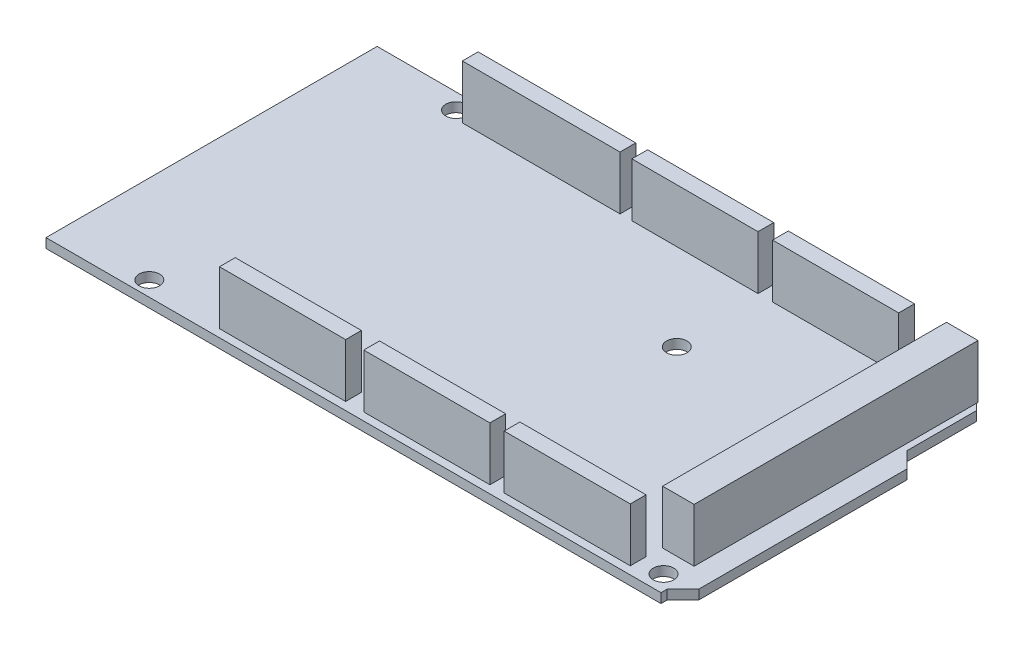
SolidWorks part; units mm, degrees
ref_plane "Front Plane" through (0, 0, 0) normal (0, 0, 1) x (1, 0, 0)
ref_plane "Top Plane" through (0, 0, 0) normal (0, 1, 0) x (1, 0, 0)
ref_plane "Right Plane" through (0, 0, 0) normal (1, 0, 0) x (0, 0, -1)
sketch "Sketch1" plane through (0, 0, 0) normal (0, 1, 0) x (1, 0, 0)
  line L0 (99.06, 39.608) -> (101.6, 37.068)
  line L1 (0, 0) -> (99.06, 0)
  line L2 (0, 0) -> (0, 53.34)
  line L3 (0, 53.34) -> (96.52, 53.34)
  line L4 (99.06, 0) -> (99.06, 1)
  line L5 (101.6, 37.068) -> (101.6, 3.54)
  line L6 (101.6, 3.54) -> (99.06, 1)
  line L7 (99.06, 39.608) -> (99.06, 50.8)
  line L8 (96.52, 53.34) -> (99.06, 50.8)
  point P1 (99.06, 53.34)
  dimension "D1" = 99.06
  dimension "D2" = 53.34
  dimension "D3" = 101.6
  dimension "D4" = 38.608
  dimension "D5" = 1
extrude "Boss-Extrude1" add sketch "Sketch1" along normal mid plane 1.524
hole_wizard "Ø1.3 (1.3) Diameter Hole1" positions "Sketch2" profile "Sketch3" hole size "Ø1.3" standard "ANSI Metric" end condition up to next
sketch "Sketch2" plane through (0, 0.762, 0) normal (0, 1, 0) x (1, 0, 0)
  line L0 (0, 53.34) -> (0, 0) construction
  line L1 (0, 0) -> (99.06, 0) construction
  line L2 (27.94, 0) -> (27.94, 2.54) construction
  line L5 (18.796, 50.8) -> (18.796, 53.34) construction
  line L6 (96.52, 53.34) -> (0, 53.34) construction
  line L9 (18.796, 50.8) -> (21.336, 50.8) construction
  line L10 (51.181, 2.54) -> (53.721, 2.54) construction
  line L11 (46.101, 50.8) -> (48.641, 50.8) construction
  line L12 (73.787, 2.54) -> (76.327, 2.54) construction
  point P0 (27.94, 2.54)
  point P2 (18.796, 50.8)
  point P25 (30.48, 2.54)
  point P26 (33.02, 2.54)
  point P27 (35.56, 2.54)
  point P28 (38.1, 2.54)
  point P29 (40.64, 2.54)
  point P30 (43.18, 2.54)
  point P31 (45.72, 2.54)
  point P36 (21.336, 50.8)
  point P37 (23.876, 50.8)
  point P38 (26.416, 50.8)
  point P39 (28.956, 50.8)
  point P40 (31.496, 50.8)
  point P41 (34.036, 50.8)
  point P42 (36.576, 50.8)
  point P43 (39.116, 50.8)
  point P44 (41.656, 50.8)
  point P47 (51.181, 2.54)
  point P49 (46.101, 50.8)
  point P56 (53.721, 2.54)
  point P57 (56.261, 2.54)
  point P58 (58.801, 2.54)
  point P59 (61.341, 2.54)
  point P60 (63.881, 2.54)
  point P61 (66.421, 2.54)
  point P62 (68.961, 2.54)
  point P71 (48.641, 50.8)
  point P72 (51.181, 50.8)
  point P73 (53.721, 50.8)
  point P74 (56.261, 50.8)
  point P75 (58.801, 50.8)
  point P76 (61.341, 50.8)
  point P77 (63.881, 50.8)
  point P80 (68.7578, 50.8)
  point P82 (73.787, 2.54)
  point P93 (71.2978, 50.8)
  point P94 (76.327, 2.54)
  point P95 (73.8378, 50.8)
  point P96 (78.867, 2.54)
  point P97 (76.3778, 50.8)
  point P98 (81.407, 2.54)
  point P99 (78.9178, 50.8)
  point P100 (83.947, 2.54)
  point P101 (81.4578, 50.8)
  point P102 (86.487, 2.54)
  point P103 (83.9978, 50.8)
  point P104 (89.027, 2.54)
  point P105 (86.5378, 50.8)
  point P106 (91.567, 2.54)
  point P109 (94.234, 50.8)
  point P111 (96.774, 50.8)
  point P122 (94.234, 48.26)
  point P123 (96.774, 48.26)
  point P124 (94.234, 45.72)
  point P125 (96.774, 45.72)
  point P126 (94.234, 43.18)
  point P127 (96.774, 43.18)
  point P128 (94.234, 40.64)
  point P129 (96.774, 40.64)
  point P130 (94.234, 38.1)
  point P131 (96.774, 38.1)
  point P132 (94.234, 35.56)
  point P133 (96.774, 35.56)
  point P134 (94.234, 33.02)
  point P135 (96.774, 33.02)
  point P136 (94.234, 30.48)
  point P137 (96.774, 30.48)
  point P138 (94.234, 27.94)
  point P139 (96.774, 27.94)
  point P140 (94.234, 25.4)
  point P141 (96.774, 25.4)
  point P142 (94.234, 22.86)
  point P143 (96.774, 22.86)
  point P144 (94.234, 20.32)
  point P145 (96.774, 20.32)
  point P146 (94.234, 17.78)
  point P147 (96.774, 17.78)
  point P148 (94.234, 15.24)
  point P149 (96.774, 15.24)
  point P150 (94.234, 12.7)
  point P151 (96.774, 12.7)
  point P152 (94.234, 10.16)
  point P153 (96.774, 10.16)
  point P154 (94.234, 7.62)
  point P155 (96.774, 7.62)
  dimension "D1" = 18.796
  dimension "D2" = 50.8
  dimension "D3" = 27.94
  dimension "D5" = 2.54
  dimension "D7" = 2.54
  dimension "D8" = 51.181
  dimension "D10" = 2.54
  dimension "D11" = 46.101
  dimension "D12" = 8
  dimension "D13" = 2.54
  dimension "D14" = 73.787
  dimension "D15" = 68.7578
  dimension "D17" = 2.54
  dimension "D18" = 2.54
  dimension "D20" = 94.234
  dimension "D4" = 8
  dimension "D6" = 10
  dimension "D9" = 8
  dimension "D16" = 8
  dimension "D19" = 18
sketch "Sketch3" plane through (27.94, 0.762, -2.54) normal (1, 0, 0) x (0, 0, 1)
  line L0 (0, 0) -> (0, 1.524)
  line L1 (0, 1.524) -> (0.65, 1.524)
  line L2 (0.65, 1.524) -> (0.65, 0)
  line L5 (0.65, 0) -> (0, 0)
  line L11 (0, -6.35) -> (0, 107.95) construction
  dimension "Thru Hole Dia." = 1.3
  dimension "Thru Hole Depth" = 1.524
hole_wizard "Ø3.3 (3.3) Diameter Hole1" positions "Sketch4" profile "Sketch5" hole size "Ø3.3" standard "ANSI Metric" end condition up to next
sketch "Sketch4" plane through (0, 0.762, 0) normal (0, 1, 0) x (1, 0, 0)
  line L0 (0, 53.34) -> (0, 0) construction
  line L1 (0, 0) -> (99.06, 0) construction
  point P0 (15.24, 50.8)
  point P2 (90.3732, 50.8)
  point P4 (96.647, 2.8094)
  point P6 (66.04, 7.366)
  point P8 (66.04, 35.56)
  point P10 (14.224, 2.413)
  dimension "D1" = 14.224
  dimension "D2" = 2.413
  dimension "D3" = 7.366
  dimension "D4" = 66.04
  dimension "D5" = 35.56
  dimension "D6" = 96.647
  dimension "D7" = 15.24
  dimension "D8" = 90.3732
  dimension "D9" = 50.8
sketch "Sketch5" plane through (15.24, 0.762, -50.8) normal (1, 0, 0) x (0, 0, 1)
  line L0 (0, 0) -> (0, 1.524)
  line L1 (0, 1.524) -> (1.65, 1.524)
  line L2 (1.65, 1.524) -> (1.65, 0)
  line L5 (1.65, 0) -> (0, 0)
  line L11 (0, -6.35) -> (0, 107.95) construction
  dimension "Thru Hole Dia." = 3.3
  dimension "Thru Hole Depth" = 1.524
sketch "Sketch6" plane through (0, 0.762, 0) normal (0, 1, 0) x (1, 0, 0)
  line L1 (17.526, 52.07) -> (42.926, 52.07)
  line L2 (17.526, 52.07) -> (17.526, 49.53)
  line L3 (17.526, 49.53) -> (42.926, 49.53)
  line L4 (42.926, 52.07) -> (42.926, 49.53)
  line L5 (44.831, 52.07) -> (65.151, 52.07)
  line L6 (44.831, 52.07) -> (44.831, 49.53)
  line L7 (44.831, 49.53) -> (65.151, 49.53)
  line L8 (65.151, 52.07) -> (65.151, 49.53)
  line L9 (67.4878, 52.07) -> (87.8078, 52.07)
  line L10 (67.4878, 52.07) -> (67.4878, 49.53)
  line L11 (67.4878, 49.53) -> (87.8078, 49.53)
  line L12 (87.8078, 52.07) -> (87.8078, 49.53)
  line L13 (92.964, 52.07) -> (98.044, 52.07)
  line L14 (92.964, 52.07) -> (92.964, 6.35)
  line L15 (92.964, 6.35) -> (98.044, 6.35)
  line L16 (98.044, 52.07) -> (98.044, 6.35)
  line L17 (92.837, 1.27) -> (72.517, 1.27)
  line L18 (92.837, 1.27) -> (92.837, 3.81)
  line L19 (92.837, 3.81) -> (72.517, 3.81)
  line L20 (72.517, 1.27) -> (72.517, 3.81)
  line L21 (26.67, 3.81) -> (46.99, 3.81)
  line L22 (26.67, 3.81) -> (26.67, 1.27)
  line L23 (26.67, 1.27) -> (46.99, 1.27)
  line L24 (46.99, 3.81) -> (46.99, 1.27)
  line L25 (49.911, 3.81) -> (70.231, 3.81)
  line L26 (49.911, 3.81) -> (49.911, 1.27)
  line L27 (49.911, 1.27) -> (70.231, 1.27)
  line L28 (70.231, 3.81) -> (70.231, 1.27)
  line L33 (41.656, 50.8) -> (42.926, 50.8) construction
  line L34 (18.796, 50.8) -> (17.526, 50.8) construction
  line L35 (46.101, 50.8) -> (44.831, 50.8) construction
  line L36 (63.881, 50.8) -> (65.151, 50.8) construction
  line L37 (68.7578, 50.8) -> (67.4878, 50.8) construction
  line L38 (86.5378, 50.8) -> (87.8078, 50.8) construction
  line L39 (94.234, 50.8) -> (92.964, 50.8) construction
  line L41 (94.234, 7.62) -> (92.964, 7.62) construction
  line L42 (27.94, 2.54) -> (26.67, 2.54) construction
  line L43 (45.72, 2.54) -> (46.99, 2.54) construction
  line L44 (49.911, 2.54) -> (51.181, 2.54) construction
  line L45 (68.961, 2.54) -> (70.231, 2.54) construction
  line L46 (72.517, 2.54) -> (73.787, 2.54) construction
  line L47 (91.567, 2.54) -> (92.837, 2.54) construction
  point P30 (18.796, 50.8)
  point P34 (27.94, 2.54)
  point P35 (94.234, 7.62)
  point P36 (94.234, 50.8)
  point P38 (86.5378, 50.8)
  point P41 (68.7578, 50.8)
  point P43 (63.881, 50.8)
  point P45 (46.101, 50.8)
  point P47 (41.656, 50.8)
  point P64 (91.567, 2.54)
  point P65 (73.787, 2.54)
  point P67 (68.961, 2.54)
  point P69 (51.181, 2.54)
  point P71 (45.72, 2.54)
  dimension "D1" = 2.54
  dimension "D2" = 5.08
  dimension "D3" = 1.27
  dimension "D4" = 1.27
extrude "Boss-Extrude2" add sketch "Sketch6" along normal blind 8.636 separate body
